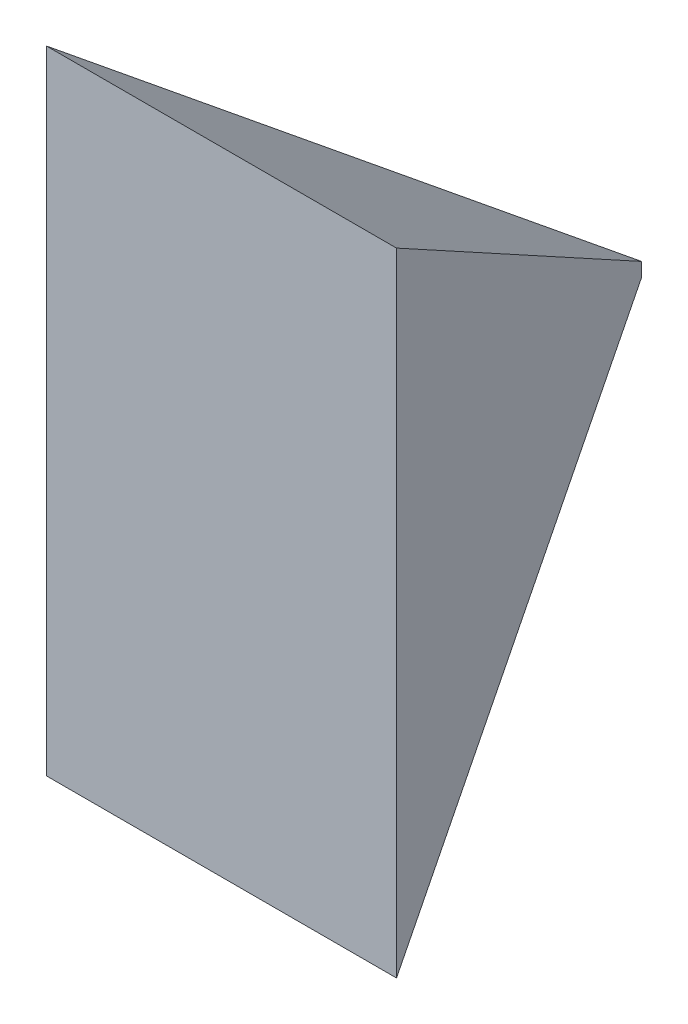
SolidWorks part; units mm, degrees
ref_plane "Front Plane" through (0, 0, 0) normal (0, 0, 1) x (1, 0, 0)
ref_plane "Top Plane" through (0, 0, 0) normal (0, 1, 0) x (1, 0, 0)
ref_plane "Right Plane" through (0, 0, 0) normal (1, 0, 0) x (0, 0, -1)
sketch "Sketch3" plane through (0, 0, 47.65) normal (0, 1, 0) x (1, 0, 0)
  line L0 (-12.5, 47.65) -> (0, 77.65)
  line L1 (0, 77.65) -> (12.5, 47.65)
  line L2 (12.5, 47.65) -> (-12.5, 47.65)
  point P6 (0, 47.65)
  dimension "D1" = 30
  dimension "D2" = 0
  dimension "D3" = 32.5
extrude "Boss-Extrude1" add sketch "Sketch3" along normal blind 45.15
sketch "Sketch4" plane through (0, 0, -4.2308) normal (1, 0, 0) x (0, 0, -1)
  line L0 (-4.2308, 45.15) -> (25.7692, 23.075)
  line L1 (25.7692, 45.15) -> (25.7692, 0) construction
  line L2 (25.7692, 23.075) -> (25.7692, 45.15)
  line L3 (-4.2308, 45.15) -> (25.7692, 45.15) construction
  line L4 (25.7692, 45.15) -> (-4.2308, 45.15)
  line L5 (-4.2308, 0) -> (25.7692, 0)
  line L6 (25.7692, 0) -> (25.7692, 22.075)
  line L7 (25.7692, 22.075) -> (-4.2308, 0)
  line L9 (-4.2308, 45.15) -> (-4.2308, 0) construction
  point P17 (-4.2308, 22.575)
  dimension "D1" = 1
  dimension "D2" = 0.5
extrude "Cut-Extrude1" cut sketch "Sketch4" against normal through all both and the other way through all
ref_plane "B Mid Plane" through (0, 22.575, 0) normal (0, -1, 0) x (-1, 0, 0)
